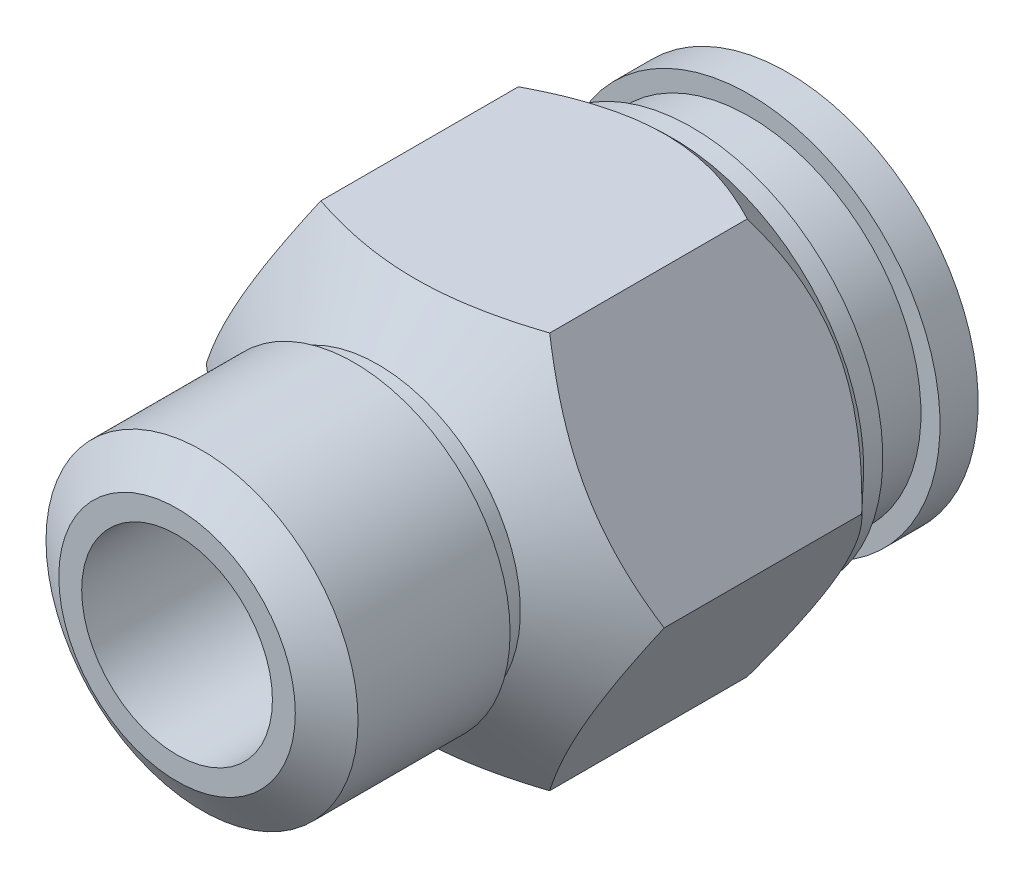
SolidWorks part; units mm, degrees
ref_plane "Alzado" through (0, 0, 0) normal (0, 0, 1) x (1, 0, 0)
ref_plane "Planta" through (0, 0, 0) normal (0, 1, 0) x (1, 0, 0)
ref_plane "Vista lateral" through (0, 0, 0) normal (1, 0, 0) x (0, 0, -1)
sketch "Croquis1" plane through (0, 0, 0) normal (0, 1, 0) x (1, 0, 0)
  line L0 (0, 34.9564) -> (0, -25.7406) construction
  line L1 (5, 26.6793) -> (10, 26.6793)
  line L2 (10, 26.6793) -> (10, 24.6793)
  line L3 (10, 24.6793) -> (9, 24.6793)
  line L4 (9, 24.6793) -> (9, 21.6793)
  line L5 (9, 21.6793) -> (10, 21.6793)
  line L6 (10, 21.6793) -> (10, 20.6793)
  line L7 (10, 20.6793) -> (12, 18.5748)
  line L8 (12, 18.5748) -> (12, 8.2155)
  line L9 (12, 8.2155) -> (7.4643, 5.2155)
  line L10 (7.4643, 5.2155) -> (7.4643, 4.4394)
  line L11 (7.4643, 4.4394) -> (8.1794, 3.9619)
  line L12 (8.1794, 3.9619) -> (8.1794, -4.0116)
  line L13 (8.1794, -4.0116) -> (6.2001, -5.3207)
  line L14 (6.2001, -5.3207) -> (5, -5.3207)
  line L15 (5, -5.3207) -> (5, 26.6793)
  dimension "D1" = 12
  dimension "D2" = 10
  dimension "D3" = 9
  dimension "D4" = 1
  dimension "D5" = 1
  dimension "D6" = 3
  dimension "D7" = 1
  dimension "2" = 2
  dimension "D8" = 2.1044
  dimension "D9" = 3
  dimension "D10" = 0.7761
  dimension "D11" = 32
  dimension "D12" = 5
revolve "Revolución1" add sketch "Croquis1" angle 360 about L0
sketch "Croquis2" plane through (0, 0, 0) normal (0, 0, 1) x (1, 0, 0)
  line L1 (12, 0) -> (6, 10.3923)
  line L2 (6, 10.3923) -> (-6, 10.3923)
  line L3 (-6, 10.3923) -> (-12, 0)
  line L4 (-12, 0) -> (-6, -10.3923)
  line L5 (-6, -10.3923) -> (6, -10.3923)
  line L6 (6, -10.3923) -> (12, 0)
  circle A0 centre (0, 0) radius 10.3923 construction
extrude "Cortar-Extruir2" cut sketch "Croquis2" against normal blind 40 flip side to cut
